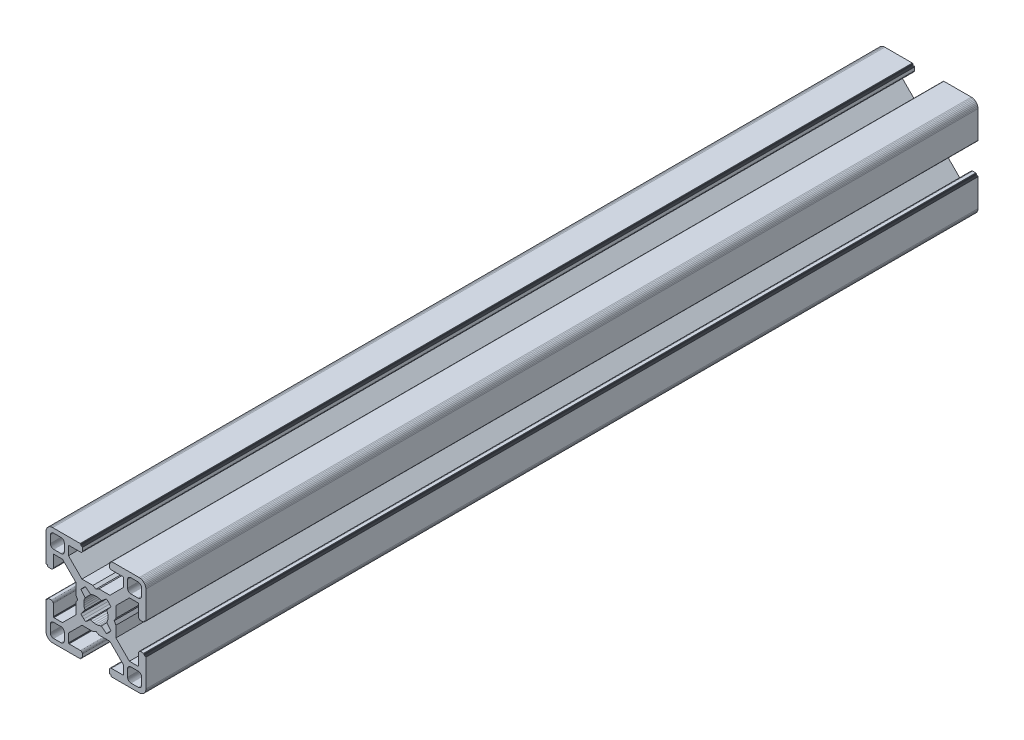
SolidWorks part; units mm, degrees
ref_plane "Front Plane" through (0, 0, 0) normal (0, 0, 1) x (1, 0, 0)
ref_plane "Top Plane" through (0, 0, 0) normal (0, 1, 0) x (1, 0, 0)
ref_plane "Right Plane" through (0, 0, 0) normal (1, 0, 0) x (0, 0, -1)
ref_plane "Plane1" through (0, 0, 0) normal (0, 0, 1) x (1, 0, 0)
sketch "Sketch1" plane through (0, 0, 0) normal (0, 0, 1) x (1, 0, 0)
  line L0 (28.3473, 29.9696) -> (28, 30)
  line L1 (28, 30) -> (19.75, 30)
  line L2 (19.75, 30) -> (19.7153, 29.997)
  line L3 (19.7153, 29.997) -> (19.6816, 29.9879)
  line L4 (19.6816, 29.9879) -> (19.65, 29.9732)
  line L5 (19.65, 29.9732) -> (19.6214, 29.9532)
  line L6 (19.6214, 29.9532) -> (19.5968, 29.9286)
  line L7 (19.5968, 29.9286) -> (19.5768, 29.9)
  line L8 (19.5768, 29.9) -> (19.5621, 29.8684)
  line L9 (19.5621, 29.8684) -> (19.553, 29.8347)
  line L10 (19.553, 29.8347) -> (19.55, 29.8)
  line L11 (19.55, 29.8) -> (19.55, 29.7)
  line L12 (19.55, 29.7) -> (19.547, 29.6653)
  line L13 (19.547, 29.6653) -> (19.5379, 29.6316)
  line L14 (19.5379, 29.6316) -> (19.5232, 29.6)
  line L15 (19.5232, 29.6) -> (19.5032, 29.5714)
  line L16 (19.5032, 29.5714) -> (19.4786, 29.5468)
  line L17 (19.4786, 29.5468) -> (19.45, 29.5268)
  line L18 (19.45, 29.5268) -> (19.4184, 29.5121)
  line L19 (19.4184, 29.5121) -> (19.3847, 29.503)
  line L20 (19.3847, 29.503) -> (19.35, 29.5)
  line L21 (19.35, 29.5) -> (19.25, 29.5)
  line L22 (19.25, 29.5) -> (19.2153, 29.497)
  line L23 (19.2153, 29.497) -> (19.1816, 29.4879)
  line L24 (19.1816, 29.4879) -> (19.15, 29.4732)
  line L25 (19.15, 29.4732) -> (19.1214, 29.4532)
  line L26 (19.1214, 29.4532) -> (19.0968, 29.4286)
  line L27 (19.0968, 29.4286) -> (19.0768, 29.4)
  line L28 (19.0768, 29.4) -> (19.0621, 29.3684)
  line L29 (19.0621, 29.3684) -> (19.053, 29.3347)
  line L30 (19.053, 29.3347) -> (19.05, 29.3)
  line L31 (19.05, 29.3) -> (19.05, 28.4)
  line L32 (19.05, 28.4) -> (19.0591, 28.2958)
  line L33 (19.0591, 28.2958) -> (19.0862, 28.1948)
  line L34 (19.0862, 28.1948) -> (19.1304, 28.1)
  line L35 (19.1304, 28.1) -> (19.1904, 28.0143)
  line L36 (19.1904, 28.0143) -> (19.2643, 27.9404)
  line L37 (19.2643, 27.9404) -> (19.35, 27.8804)
  line L38 (19.35, 27.8804) -> (19.4448, 27.8362)
  line L39 (19.4448, 27.8362) -> (19.5458, 27.8091)
  line L40 (19.5458, 27.8091) -> (19.65, 27.8)
  line L41 (19.65, 27.8) -> (23.05, 27.8)
  line L42 (23.05, 27.8) -> (23.0847, 27.7969)
  line L43 (23.0847, 27.7969) -> (23.1184, 27.7879)
  line L44 (23.1184, 27.7879) -> (23.15, 27.7732)
  line L45 (23.15, 27.7732) -> (23.1786, 27.7532)
  line L46 (23.1786, 27.7532) -> (23.2032, 27.7285)
  line L47 (23.2032, 27.7285) -> (23.2232, 27.7)
  line L48 (23.2232, 27.7) -> (23.2379, 27.6684)
  line L49 (23.2379, 27.6684) -> (23.247, 27.6347)
  line L50 (23.247, 27.6347) -> (23.25, 27.6)
  line L51 (23.25, 27.6) -> (23.25, 25.05)
  line L52 (23.25, 25.05) -> (19.2045, 21)
  line L53 (19.2045, 21) -> (15.9, 21)
  line L54 (15.9, 21) -> (15, 20.4848)
  line L55 (15, 20.4848) -> (14.1, 21)
  line L56 (14.1, 21) -> (10.7955, 21)
  line L57 (10.7955, 21) -> (7.9973, 23.8013)
  line L58 (7.9973, 23.8013) -> (6.75, 25.05)
  line L59 (6.75, 25.05) -> (6.75, 27.6)
  line L60 (6.75, 27.6) -> (6.753, 27.6347)
  line L61 (6.753, 27.6347) -> (6.7621, 27.6684)
  line L62 (6.7621, 27.6684) -> (6.7768, 27.7)
  line L63 (6.7768, 27.7) -> (6.7968, 27.7285)
  line L64 (6.7968, 27.7285) -> (6.8215, 27.7532)
  line L65 (6.8215, 27.7532) -> (6.85, 27.7732)
  line L66 (6.85, 27.7732) -> (6.8816, 27.7879)
  line L67 (6.8816, 27.7879) -> (6.9153, 27.7969)
  line L68 (6.9153, 27.7969) -> (6.95, 27.8)
  line L69 (6.95, 27.8) -> (10.35, 27.8)
  line L70 (10.35, 27.8) -> (10.4542, 27.8091)
  line L71 (10.4542, 27.8091) -> (10.5552, 27.8362)
  line L72 (10.5552, 27.8362) -> (10.65, 27.8804)
  line L73 (10.65, 27.8804) -> (10.7357, 27.9404)
  line L74 (10.7357, 27.9404) -> (10.8096, 28.0143)
  line L75 (10.8096, 28.0143) -> (10.8696, 28.1)
  line L76 (10.8696, 28.1) -> (10.9138, 28.1948)
  line L77 (10.9138, 28.1948) -> (10.9409, 28.2958)
  line L78 (10.9409, 28.2958) -> (10.95, 28.4)
  line L79 (10.95, 28.4) -> (10.95, 29.3)
  line L80 (10.95, 29.3) -> (10.947, 29.3347)
  line L81 (10.947, 29.3347) -> (10.938, 29.3684)
  line L82 (10.938, 29.3684) -> (10.9232, 29.4)
  line L83 (10.9232, 29.4) -> (10.9032, 29.4286)
  line L84 (10.9032, 29.4286) -> (10.8786, 29.4532)
  line L85 (10.8786, 29.4532) -> (10.85, 29.4732)
  line L86 (10.85, 29.4732) -> (10.8184, 29.4879)
  line L87 (10.8184, 29.4879) -> (10.7847, 29.497)
  line L88 (10.7847, 29.497) -> (10.75, 29.5)
  line L89 (10.75, 29.5) -> (10.65, 29.5)
  line L90 (10.65, 29.5) -> (10.6153, 29.503)
  line L91 (10.6153, 29.503) -> (10.5816, 29.5121)
  line L92 (10.5816, 29.5121) -> (10.55, 29.5268)
  line L93 (10.55, 29.5268) -> (10.5214, 29.5468)
  line L94 (10.5214, 29.5468) -> (10.4968, 29.5714)
  line L95 (10.4968, 29.5714) -> (10.4768, 29.6)
  line L96 (10.4768, 29.6) -> (10.4621, 29.6316)
  line L97 (10.4621, 29.6316) -> (10.453, 29.6653)
  line L98 (10.453, 29.6653) -> (10.45, 29.7)
  line L99 (10.45, 29.7) -> (10.45, 29.8)
  line L100 (10.45, 29.8) -> (10.447, 29.8347)
  line L101 (10.447, 29.8347) -> (10.4379, 29.8684)
  line L102 (10.4379, 29.8684) -> (10.4232, 29.9)
  line L103 (10.4232, 29.9) -> (10.4032, 29.9286)
  line L104 (10.4032, 29.9286) -> (10.3786, 29.9532)
  line L105 (10.3786, 29.9532) -> (10.35, 29.9732)
  line L106 (10.35, 29.9732) -> (10.3184, 29.9879)
  line L107 (10.3184, 29.9879) -> (10.2847, 29.997)
  line L108 (10.2847, 29.997) -> (10.25, 30)
  line L109 (10.25, 30) -> (2, 30)
  line L110 (2, 30) -> (1.6527, 29.9696)
  line L111 (1.6527, 29.9696) -> (1.316, 29.8794)
  line L112 (1.316, 29.8794) -> (1, 29.7321)
  line L113 (1, 29.7321) -> (0.7144, 29.5321)
  line L114 (0.7144, 29.5321) -> (0.4679, 29.2856)
  line L115 (0.4679, 29.2856) -> (0.2679, 29)
  line L116 (0.2679, 29) -> (0.1206, 28.684)
  line L117 (0.1206, 28.684) -> (0.0304, 28.3473)
  line L118 (0.0304, 28.3473) -> (0, 28)
  line L119 (0, 28) -> (0, 19.75)
  line L120 (0, 19.75) -> (0.003, 19.7153)
  line L121 (0.003, 19.7153) -> (0.0121, 19.6816)
  line L122 (0.0121, 19.6816) -> (0.0268, 19.65)
  line L123 (0.0268, 19.65) -> (0.0468, 19.6214)
  line L124 (0.0468, 19.6214) -> (0.0714, 19.5968)
  line L125 (0.0714, 19.5968) -> (0.1, 19.5768)
  line L126 (0.1, 19.5768) -> (0.1316, 19.5621)
  line L127 (0.1316, 19.5621) -> (0.1653, 19.553)
  line L128 (0.1653, 19.553) -> (0.2, 19.55)
  line L129 (0.2, 19.55) -> (0.3, 19.55)
  line L130 (0.3, 19.55) -> (0.3347, 19.547)
  line L131 (0.3347, 19.547) -> (0.3684, 19.5379)
  line L132 (0.3684, 19.5379) -> (0.4, 19.5232)
  line L133 (0.4, 19.5232) -> (0.4286, 19.5032)
  line L134 (0.4286, 19.5032) -> (0.4532, 19.4786)
  line L135 (0.4532, 19.4786) -> (0.4732, 19.45)
  line L136 (0.4732, 19.45) -> (0.4879, 19.4184)
  line L137 (0.4879, 19.4184) -> (0.497, 19.3847)
  line L138 (0.497, 19.3847) -> (0.5, 19.35)
  line L139 (0.5, 19.35) -> (0.5, 19.25)
  line L140 (0.5, 19.25) -> (0.503, 19.2153)
  line L141 (0.503, 19.2153) -> (0.5121, 19.1816)
  line L142 (0.5121, 19.1816) -> (0.5268, 19.15)
  line L143 (0.5268, 19.15) -> (0.5468, 19.1214)
  line L144 (0.5468, 19.1214) -> (0.5714, 19.0968)
  line L145 (0.5714, 19.0968) -> (0.6, 19.0768)
  line L146 (0.6, 19.0768) -> (0.6316, 19.0621)
  line L147 (0.6316, 19.0621) -> (0.6653, 19.053)
  line L148 (0.6653, 19.053) -> (0.7, 19.05)
  line L149 (0.7, 19.05) -> (1.6, 19.05)
  line L150 (1.6, 19.05) -> (1.7042, 19.0591)
  line L151 (1.7042, 19.0591) -> (1.8052, 19.0862)
  line L152 (1.8052, 19.0862) -> (1.9, 19.1304)
  line L153 (1.9, 19.1304) -> (1.9857, 19.1904)
  line L154 (1.9857, 19.1904) -> (2.0596, 19.2643)
  line L155 (2.0596, 19.2643) -> (2.1196, 19.35)
  line L156 (2.1196, 19.35) -> (2.1638, 19.4448)
  line L157 (2.1638, 19.4448) -> (2.1909, 19.5458)
  line L158 (2.1909, 19.5458) -> (2.2, 19.65)
  line L159 (2.2, 19.65) -> (2.2, 23.05)
  line L160 (2.2, 23.05) -> (2.203, 23.0847)
  line L161 (2.203, 23.0847) -> (2.2121, 23.1184)
  line L162 (2.2121, 23.1184) -> (2.2268, 23.15)
  line L163 (2.2268, 23.15) -> (2.2468, 23.1786)
  line L164 (2.2468, 23.1786) -> (2.2714, 23.2032)
  line L165 (2.2714, 23.2032) -> (2.3, 23.2232)
  line L166 (2.3, 23.2232) -> (2.3316, 23.2379)
  line L167 (2.3316, 23.2379) -> (2.3653, 23.247)
  line L168 (2.3653, 23.247) -> (2.4, 23.25)
  line L169 (2.4, 23.25) -> (4.95, 23.25)
  line L170 (4.95, 23.25) -> (7.9973, 20.2027)
  line L171 (7.9973, 20.2027) -> (8.9955, 19.2045)
  line L172 (8.9955, 19.2045) -> (8.9955, 15.9)
  line L173 (8.9955, 15.9) -> (9.5151, 15)
  line L174 (9.5151, 15) -> (8.9955, 14.1)
  line L175 (8.9955, 14.1) -> (8.9955, 10.7955)
  line L176 (8.9955, 10.7955) -> (4.95, 6.75)
  line L177 (4.95, 6.75) -> (2.4, 6.75)
  line L178 (2.4, 6.75) -> (2.3653, 6.753)
  line L179 (2.3653, 6.753) -> (2.3316, 6.7621)
  line L180 (2.3316, 6.7621) -> (2.3, 6.7768)
  line L181 (2.3, 6.7768) -> (2.2714, 6.7968)
  line L182 (2.2714, 6.7968) -> (2.2468, 6.8214)
  line L183 (2.2468, 6.8214) -> (2.2268, 6.85)
  line L184 (2.2268, 6.85) -> (2.2121, 6.8816)
  line L185 (2.2121, 6.8816) -> (2.203, 6.9153)
  line L186 (2.203, 6.9153) -> (2.2, 6.95)
  line L187 (2.2, 6.95) -> (2.2, 10.35)
  line L188 (2.2, 10.35) -> (2.1909, 10.4542)
  line L189 (2.1909, 10.4542) -> (2.1638, 10.5552)
  line L190 (2.1638, 10.5552) -> (2.1196, 10.65)
  line L191 (2.1196, 10.65) -> (2.0596, 10.7357)
  line L192 (2.0596, 10.7357) -> (1.9857, 10.8096)
  line L193 (1.9857, 10.8096) -> (1.9, 10.8696)
  line L194 (1.9, 10.8696) -> (1.8052, 10.9138)
  line L195 (1.8052, 10.9138) -> (1.7042, 10.9409)
  line L196 (1.7042, 10.9409) -> (1.6, 10.95)
  line L197 (1.6, 10.95) -> (0.7, 10.95)
  line L198 (0.7, 10.95) -> (0.6653, 10.9469)
  line L199 (0.6653, 10.9469) -> (0.6316, 10.9379)
  line L200 (0.6316, 10.9379) -> (0.6, 10.9232)
  line L201 (0.6, 10.9232) -> (0.5715, 10.9032)
  line L202 (0.5715, 10.9032) -> (0.5468, 10.8785)
  line L203 (0.5468, 10.8785) -> (0.5268, 10.85)
  line L204 (0.5268, 10.85) -> (0.5121, 10.8184)
  line L205 (0.5121, 10.8184) -> (0.503, 10.7847)
  line L206 (0.503, 10.7847) -> (0.5, 10.75)
  line L207 (0.5, 10.75) -> (0.5, 10.65)
  line L208 (0.5, 10.65) -> (0.497, 10.6153)
  line L209 (0.497, 10.6153) -> (0.4879, 10.5816)
  line L210 (0.4879, 10.5816) -> (0.4732, 10.55)
  line L211 (0.4732, 10.55) -> (0.4532, 10.5214)
  line L212 (0.4532, 10.5214) -> (0.4286, 10.4968)
  line L213 (0.4286, 10.4968) -> (0.4, 10.4768)
  line L214 (0.4, 10.4768) -> (0.3684, 10.4621)
  line L215 (0.3684, 10.4621) -> (0.3347, 10.453)
  line L216 (0.3347, 10.453) -> (0.3, 10.45)
  line L217 (0.3, 10.45) -> (0.2, 10.45)
  line L218 (0.2, 10.45) -> (0.1653, 10.447)
  line L219 (0.1653, 10.447) -> (0.1316, 10.4379)
  line L220 (0.1316, 10.4379) -> (0.1, 10.4232)
  line L221 (0.1, 10.4232) -> (0.0714, 10.4032)
  line L222 (0.0714, 10.4032) -> (0.0468, 10.3786)
  line L223 (0.0468, 10.3786) -> (0.0268, 10.35)
  line L224 (0.0268, 10.35) -> (0.0121, 10.3184)
  line L225 (0.0121, 10.3184) -> (0.003, 10.2847)
  line L226 (0.003, 10.2847) -> (0, 10.25)
  line L227 (0, 10.25) -> (0, 2)
  line L228 (0, 2) -> (0.0304, 1.6527)
  line L229 (0.0304, 1.6527) -> (0.1206, 1.316)
  line L230 (0.1206, 1.316) -> (0.2679, 1)
  line L231 (0.2679, 1) -> (0.4679, 0.7144)
  line L232 (0.4679, 0.7144) -> (0.7144, 0.4679)
  line L233 (0.7144, 0.4679) -> (1, 0.2679)
  line L234 (1, 0.2679) -> (1.316, 0.1206)
  line L235 (1.316, 0.1206) -> (1.6527, 0.0304)
  line L236 (1.6527, 0.0304) -> (2, 0)
  line L237 (2, 0) -> (10.25, 0)
  line L238 (10.25, 0) -> (10.2847, 0.003)
  line L239 (10.2847, 0.003) -> (10.3184, 0.0121)
  line L240 (10.3184, 0.0121) -> (10.35, 0.0268)
  line L241 (10.35, 0.0268) -> (10.3786, 0.0468)
  line L242 (10.3786, 0.0468) -> (10.4032, 0.0714)
  line L243 (10.4032, 0.0714) -> (10.4232, 0.1)
  line L244 (10.4232, 0.1) -> (10.4379, 0.1316)
  line L245 (10.4379, 0.1316) -> (10.447, 0.1653)
  line L246 (10.447, 0.1653) -> (10.45, 0.2)
  line L247 (10.45, 0.2) -> (10.45, 0.3)
  line L248 (10.45, 0.3) -> (10.453, 0.3347)
  line L249 (10.453, 0.3347) -> (10.4621, 0.3684)
  line L250 (10.4621, 0.3684) -> (10.4768, 0.4)
  line L251 (10.4768, 0.4) -> (10.4968, 0.4286)
  line L252 (10.4968, 0.4286) -> (10.5214, 0.4532)
  line L253 (10.5214, 0.4532) -> (10.55, 0.4732)
  line L254 (10.55, 0.4732) -> (10.5816, 0.4879)
  line L255 (10.5816, 0.4879) -> (10.6153, 0.497)
  line L256 (10.6153, 0.497) -> (10.65, 0.5)
  line L257 (10.65, 0.5) -> (10.75, 0.5)
  line L258 (10.75, 0.5) -> (10.7847, 0.503)
  line L259 (10.7847, 0.503) -> (10.8184, 0.5121)
  line L260 (10.8184, 0.5121) -> (10.85, 0.5268)
  line L261 (10.85, 0.5268) -> (10.8785, 0.5468)
  line L262 (10.8785, 0.5468) -> (10.9032, 0.5715)
  line L263 (10.9032, 0.5715) -> (10.9232, 0.6)
  line L264 (10.9232, 0.6) -> (10.9379, 0.6316)
  line L265 (10.9379, 0.6316) -> (10.9469, 0.6653)
  line L266 (10.9469, 0.6653) -> (10.95, 0.7)
  line L267 (10.95, 0.7) -> (10.95, 1.6)
  line L268 (10.95, 1.6) -> (10.9409, 1.7042)
  line L269 (10.9409, 1.7042) -> (10.9138, 1.8052)
  line L270 (10.9138, 1.8052) -> (10.8696, 1.9)
  line L271 (10.8696, 1.9) -> (10.8096, 1.9857)
  line L272 (10.8096, 1.9857) -> (10.7357, 2.0596)
  line L273 (10.7357, 2.0596) -> (10.65, 2.1196)
  line L274 (10.65, 2.1196) -> (10.5552, 2.1638)
  line L275 (10.5552, 2.1638) -> (10.4542, 2.1909)
  line L276 (10.4542, 2.1909) -> (10.35, 2.2)
  line L277 (10.35, 2.2) -> (6.95, 2.2)
  line L278 (6.95, 2.2) -> (6.9153, 2.203)
  line L279 (6.9153, 2.203) -> (6.8816, 2.212)
  line L280 (6.8816, 2.212) -> (6.85, 2.2268)
  line L281 (6.85, 2.2268) -> (6.8215, 2.2468)
  line L282 (6.8215, 2.2468) -> (6.7968, 2.2714)
  line L283 (6.7968, 2.2714) -> (6.7768, 2.3)
  line L284 (6.7768, 2.3) -> (6.7621, 2.3316)
  line L285 (6.7621, 2.3316) -> (6.753, 2.3653)
  line L286 (6.753, 2.3653) -> (6.75, 2.4)
  line L287 (6.75, 2.4) -> (6.75, 4.95)
  line L288 (6.75, 4.95) -> (9.7875, 7.9908)
  line L289 (9.7875, 7.9908) -> (10.7955, 9)
  line L290 (10.7955, 9) -> (14.1, 9)
  line L291 (14.1, 9) -> (15, 9.5151)
  line L292 (15, 9.5151) -> (15.9, 9)
  line L293 (15.9, 9) -> (19.2045, 9)
  line L294 (19.2045, 9) -> (20.2126, 7.9908)
  line L295 (20.2126, 7.9908) -> (23.25, 4.95)
  line L296 (23.25, 4.95) -> (23.25, 2.4)
  line L297 (23.25, 2.4) -> (23.247, 2.3653)
  line L298 (23.247, 2.3653) -> (23.2379, 2.3316)
  line L299 (23.2379, 2.3316) -> (23.2232, 2.3)
  line L300 (23.2232, 2.3) -> (23.2032, 2.2714)
  line L301 (23.2032, 2.2714) -> (23.1786, 2.2468)
  line L302 (23.1786, 2.2468) -> (23.15, 2.2268)
  line L303 (23.15, 2.2268) -> (23.1184, 2.212)
  line L304 (23.1184, 2.212) -> (23.0847, 2.203)
  line L305 (23.0847, 2.203) -> (23.05, 2.2)
  line L306 (23.05, 2.2) -> (19.65, 2.2)
  line L307 (19.65, 2.2) -> (19.5458, 2.1909)
  line L308 (19.5458, 2.1909) -> (19.4448, 2.1638)
  line L309 (19.4448, 2.1638) -> (19.35, 2.1196)
  line L310 (19.35, 2.1196) -> (19.2643, 2.0596)
  line L311 (19.2643, 2.0596) -> (19.1904, 1.9857)
  line L312 (19.1904, 1.9857) -> (19.1304, 1.9)
  line L313 (19.1304, 1.9) -> (19.0862, 1.8052)
  line L314 (19.0862, 1.8052) -> (19.0591, 1.7042)
  line L315 (19.0591, 1.7042) -> (19.05, 1.6)
  line L316 (19.05, 1.6) -> (19.05, 0.7)
  line L317 (19.05, 0.7) -> (19.053, 0.6653)
  line L318 (19.053, 0.6653) -> (19.0621, 0.6316)
  line L319 (19.0621, 0.6316) -> (19.0768, 0.6)
  line L320 (19.0768, 0.6) -> (19.0968, 0.5714)
  line L321 (19.0968, 0.5714) -> (19.1214, 0.5468)
  line L322 (19.1214, 0.5468) -> (19.15, 0.5268)
  line L323 (19.15, 0.5268) -> (19.1816, 0.5121)
  line L324 (19.1816, 0.5121) -> (19.2153, 0.503)
  line L325 (19.2153, 0.503) -> (19.25, 0.5)
  line L326 (19.25, 0.5) -> (19.35, 0.5)
  line L327 (19.35, 0.5) -> (19.3847, 0.497)
  line L328 (19.3847, 0.497) -> (19.4184, 0.4879)
  line L329 (19.4184, 0.4879) -> (19.45, 0.4732)
  line L330 (19.45, 0.4732) -> (19.4786, 0.4532)
  line L331 (19.4786, 0.4532) -> (19.5032, 0.4286)
  line L332 (19.5032, 0.4286) -> (19.5232, 0.4)
  line L333 (19.5232, 0.4) -> (19.5379, 0.3684)
  line L334 (19.5379, 0.3684) -> (19.547, 0.3347)
  line L335 (19.547, 0.3347) -> (19.55, 0.3)
  line L336 (19.55, 0.3) -> (19.55, 0.2)
  line L337 (19.55, 0.2) -> (19.553, 0.1653)
  line L338 (19.553, 0.1653) -> (19.5621, 0.1316)
  line L339 (19.5621, 0.1316) -> (19.5768, 0.1)
  line L340 (19.5768, 0.1) -> (19.5968, 0.0714)
  line L341 (19.5968, 0.0714) -> (19.6214, 0.0468)
  line L342 (19.6214, 0.0468) -> (19.65, 0.0268)
  line L343 (19.65, 0.0268) -> (19.6816, 0.0121)
  line L344 (19.6816, 0.0121) -> (19.7153, 0.003)
  line L345 (19.7153, 0.003) -> (19.75, 0)
  line L346 (19.75, 0) -> (28, 0)
  line L347 (28, 0) -> (28.3473, 0.0304)
  line L348 (28.3473, 0.0304) -> (28.684, 0.1206)
  line L349 (28.684, 0.1206) -> (29, 0.2679)
  line L350 (29, 0.2679) -> (29.2856, 0.4679)
  line L351 (29.2856, 0.4679) -> (29.5321, 0.7144)
  line L352 (29.5321, 0.7144) -> (29.7321, 1)
  line L353 (29.7321, 1) -> (29.8794, 1.316)
  line L354 (29.8794, 1.316) -> (29.9696, 1.6527)
  line L355 (29.9696, 1.6527) -> (30, 2)
  line L356 (30, 2) -> (30, 10.25)
  line L357 (30, 10.25) -> (29.997, 10.2847)
  line L358 (29.997, 10.2847) -> (29.988, 10.3184)
  line L359 (29.988, 10.3184) -> (29.9732, 10.35)
  line L360 (29.9732, 10.35) -> (29.9532, 10.3785)
  line L361 (29.9532, 10.3785) -> (29.9286, 10.4032)
  line L362 (29.9286, 10.4032) -> (29.9, 10.4232)
  line L363 (29.9, 10.4232) -> (29.8684, 10.4379)
  line L364 (29.8684, 10.4379) -> (29.8347, 10.447)
  line L365 (29.8347, 10.447) -> (29.8, 10.45)
  line L366 (29.8, 10.45) -> (29.7, 10.45)
  line L367 (29.7, 10.45) -> (29.6649, 10.4534)
  line L368 (29.6649, 10.4534) -> (29.6312, 10.4624)
  line L369 (29.6312, 10.4624) -> (29.5996, 10.4772)
  line L370 (29.5996, 10.4772) -> (29.5711, 10.4972)
  line L371 (29.5711, 10.4972) -> (29.5464, 10.5218)
  line L372 (29.5464, 10.5218) -> (29.5264, 10.5504)
  line L373 (29.5264, 10.5504) -> (29.5117, 10.582)
  line L374 (29.5117, 10.582) -> (29.5027, 10.6156)
  line L375 (29.5027, 10.6156) -> (29.4996, 10.6504)
  line L376 (29.4996, 10.6504) -> (29.4996, 10.7504)
  line L377 (29.4996, 10.7504) -> (29.497, 10.7847)
  line L378 (29.497, 10.7847) -> (29.4879, 10.8184)
  line L379 (29.4879, 10.8184) -> (29.4732, 10.85)
  line L380 (29.4732, 10.85) -> (29.4532, 10.8785)
  line L381 (29.4532, 10.8785) -> (29.4286, 10.9032)
  line L382 (29.4286, 10.9032) -> (29.4, 10.9232)
  line L383 (29.4, 10.9232) -> (29.3684, 10.9379)
  line L384 (29.3684, 10.9379) -> (29.3347, 10.9469)
  line L385 (29.3347, 10.9469) -> (29.3, 10.95)
  line L386 (29.3, 10.95) -> (28.4, 10.95)
  line L387 (28.4, 10.95) -> (28.2958, 10.9409)
  line L388 (28.2958, 10.9409) -> (28.1948, 10.9138)
  line L389 (28.1948, 10.9138) -> (28.1, 10.8696)
  line L390 (28.1, 10.8696) -> (28.0143, 10.8096)
  line L391 (28.0143, 10.8096) -> (27.9404, 10.7357)
  line L392 (27.9404, 10.7357) -> (27.8804, 10.65)
  line L393 (27.8804, 10.65) -> (27.8362, 10.5552)
  line L394 (27.8362, 10.5552) -> (27.8091, 10.4542)
  line L395 (27.8091, 10.4542) -> (27.8, 10.35)
  line L396 (27.8, 10.35) -> (27.8, 6.95)
  line L397 (27.8, 6.95) -> (27.797, 6.9153)
  line L398 (27.797, 6.9153) -> (27.7879, 6.8816)
  line L399 (27.7879, 6.8816) -> (27.7732, 6.85)
  line L400 (27.7732, 6.85) -> (27.7532, 6.8214)
  line L401 (27.7532, 6.8214) -> (27.7286, 6.7968)
  line L402 (27.7286, 6.7968) -> (27.7, 6.7768)
  line L403 (27.7, 6.7768) -> (27.6684, 6.7621)
  line L404 (27.6684, 6.7621) -> (27.6347, 6.753)
  line L405 (27.6347, 6.753) -> (27.6, 6.75)
  line L406 (27.6, 6.75) -> (25.05, 6.75)
  line L407 (25.05, 6.75) -> (23.8092, 7.9908)
  line L408 (23.8092, 7.9908) -> (21.0045, 10.7955)
  line L409 (21.0045, 10.7955) -> (21.0045, 14.1)
  line L410 (21.0045, 14.1) -> (20.4849, 15)
  line L411 (20.4849, 15) -> (21.0045, 15.9)
  line L412 (21.0045, 15.9) -> (21.0045, 19.2045)
  line L413 (21.0045, 19.2045) -> (25.05, 23.25)
  line L414 (25.05, 23.25) -> (27.6, 23.25)
  line L415 (27.6, 23.25) -> (27.6347, 23.247)
  line L416 (27.6347, 23.247) -> (27.6684, 23.2379)
  line L417 (27.6684, 23.2379) -> (27.7, 23.2232)
  line L418 (27.7, 23.2232) -> (27.7286, 23.2032)
  line L419 (27.7286, 23.2032) -> (27.7532, 23.1786)
  line L420 (27.7532, 23.1786) -> (27.7732, 23.15)
  line L421 (27.7732, 23.15) -> (27.7879, 23.1184)
  line L422 (27.7879, 23.1184) -> (27.797, 23.0847)
  line L423 (27.797, 23.0847) -> (27.8, 23.05)
  line L424 (27.8, 23.05) -> (27.8, 19.65)
  line L425 (27.8, 19.65) -> (27.8091, 19.5458)
  line L426 (27.8091, 19.5458) -> (27.8362, 19.4448)
  line L427 (27.8362, 19.4448) -> (27.8804, 19.35)
  line L428 (27.8804, 19.35) -> (27.9404, 19.2643)
  line L429 (27.9404, 19.2643) -> (28.0143, 19.1904)
  line L430 (28.0143, 19.1904) -> (28.1, 19.1304)
  line L431 (28.1, 19.1304) -> (28.1948, 19.0862)
  line L432 (28.1948, 19.0862) -> (28.2958, 19.0591)
  line L433 (28.2958, 19.0591) -> (28.4, 19.05)
  line L434 (28.4, 19.05) -> (29.3, 19.05)
  line L435 (29.3, 19.05) -> (29.3347, 19.053)
  line L436 (29.3347, 19.053) -> (29.3684, 19.0621)
  line L437 (29.3684, 19.0621) -> (29.4, 19.0768)
  line L438 (29.4, 19.0768) -> (29.4282, 19.0971)
  line L439 (29.4282, 19.0971) -> (29.4528, 19.1218)
  line L440 (29.4528, 19.1218) -> (29.4728, 19.1504)
  line L441 (29.4728, 19.1504) -> (29.4876, 19.182)
  line L442 (29.4876, 19.182) -> (29.4966, 19.2156)
  line L443 (29.4966, 19.2156) -> (29.4996, 19.2504)
  line L444 (29.4996, 19.2504) -> (29.4996, 19.3504)
  line L445 (29.4996, 19.3504) -> (29.5027, 19.3851)
  line L446 (29.5027, 19.3851) -> (29.5117, 19.4188)
  line L447 (29.5117, 19.4188) -> (29.5264, 19.4504)
  line L448 (29.5264, 19.4504) -> (29.5464, 19.4789)
  line L449 (29.5464, 19.4789) -> (29.5711, 19.5036)
  line L450 (29.5711, 19.5036) -> (29.5996, 19.5236)
  line L451 (29.5996, 19.5236) -> (29.6312, 19.5383)
  line L452 (29.6312, 19.5383) -> (29.6649, 19.5473)
  line L453 (29.6649, 19.5473) -> (29.7, 19.55)
  line L454 (29.7, 19.55) -> (29.8, 19.55)
  line L455 (29.8, 19.55) -> (29.8347, 19.553)
  line L456 (29.8347, 19.553) -> (29.8684, 19.5621)
  line L457 (29.8684, 19.5621) -> (29.9, 19.5768)
  line L458 (29.9, 19.5768) -> (29.9286, 19.5968)
  line L459 (29.9286, 19.5968) -> (29.9532, 19.6214)
  line L460 (29.9532, 19.6214) -> (29.9732, 19.65)
  line L461 (29.9732, 19.65) -> (29.9879, 19.6816)
  line L462 (29.9879, 19.6816) -> (29.997, 19.7153)
  line L463 (29.997, 19.7153) -> (30, 19.75)
  line L464 (30, 19.75) -> (30, 28)
  line L465 (30, 28) -> (29.9696, 28.3473)
  line L466 (29.9696, 28.3473) -> (29.8794, 28.684)
  line L467 (29.8794, 28.684) -> (29.7321, 29)
  line L468 (29.7321, 29) -> (29.5321, 29.2856)
  line L469 (29.5321, 29.2856) -> (29.2856, 29.5321)
  line L470 (29.2856, 29.5321) -> (29, 29.7321)
  line L471 (29, 29.7321) -> (28.684, 29.8794)
  line L472 (28.684, 29.8794) -> (28.3473, 29.9696)
  line L473 (1.3, 25.5) -> (1.3, 27.7)
  line L474 (1.3, 27.7) -> (1.3123, 27.8564)
  line L475 (1.3123, 27.8564) -> (1.3489, 28.009)
  line L476 (1.3489, 28.009) -> (1.409, 28.154)
  line L477 (1.409, 28.154) -> (1.491, 28.2878)
  line L478 (1.491, 28.2878) -> (1.5929, 28.4071)
  line L479 (1.5929, 28.4071) -> (1.7122, 28.509)
  line L480 (1.7122, 28.509) -> (1.846, 28.591)
  line L481 (1.846, 28.591) -> (1.991, 28.6511)
  line L482 (1.991, 28.6511) -> (2.1436, 28.6877)
  line L483 (2.1436, 28.6877) -> (2.3, 28.7)
  line L484 (2.3, 28.7) -> (4.5, 28.7)
  line L485 (4.5, 28.7) -> (4.6564, 28.6877)
  line L486 (4.6564, 28.6877) -> (4.809, 28.6511)
  line L487 (4.809, 28.6511) -> (4.954, 28.591)
  line L488 (4.954, 28.591) -> (5.0878, 28.509)
  line L489 (5.0878, 28.509) -> (5.2071, 28.4071)
  line L490 (5.2071, 28.4071) -> (5.309, 28.2878)
  line L491 (5.309, 28.2878) -> (5.391, 28.154)
  line L492 (5.391, 28.154) -> (5.4511, 28.009)
  line L493 (5.4511, 28.009) -> (5.4877, 27.8564)
  line L494 (5.4877, 27.8564) -> (5.5, 27.7)
  line L495 (5.5, 27.7) -> (5.5, 25.5)
  line L496 (5.5, 25.5) -> (5.4877, 25.3436)
  line L497 (5.4877, 25.3436) -> (5.4511, 25.191)
  line L498 (5.4511, 25.191) -> (5.391, 25.046)
  line L499 (5.391, 25.046) -> (5.309, 24.9122)
  line L500 (5.309, 24.9122) -> (5.2071, 24.7929)
  line L501 (5.2071, 24.7929) -> (5.0878, 24.691)
  line L502 (5.0878, 24.691) -> (4.954, 24.609)
  line L503 (4.954, 24.609) -> (4.809, 24.5489)
  line L504 (4.809, 24.5489) -> (4.6564, 24.5123)
  line L505 (4.6564, 24.5123) -> (4.5, 24.5)
  line L506 (4.5, 24.5) -> (2.3, 24.5)
  line L507 (2.3, 24.5) -> (2.1436, 24.5123)
  line L508 (2.1436, 24.5123) -> (1.991, 24.5489)
  line L509 (1.991, 24.5489) -> (1.846, 24.609)
  line L510 (1.846, 24.609) -> (1.7122, 24.691)
  line L511 (1.7122, 24.691) -> (1.5929, 24.7929)
  line L512 (1.5929, 24.7929) -> (1.491, 24.9122)
  line L513 (1.491, 24.9122) -> (1.409, 25.046)
  line L514 (1.409, 25.046) -> (1.3489, 25.191)
  line L515 (1.3489, 25.191) -> (1.3123, 25.3436)
  line L516 (1.3123, 25.3436) -> (1.3, 25.5)
  line L517 (25.3436, 28.6877) -> (25.5, 28.7)
  line L518 (25.5, 28.7) -> (27.7, 28.7)
  line L519 (27.7, 28.7) -> (27.8564, 28.6877)
  line L520 (27.8564, 28.6877) -> (28.009, 28.6511)
  line L521 (28.009, 28.6511) -> (28.154, 28.591)
  line L522 (28.154, 28.591) -> (28.2878, 28.509)
  line L523 (28.2878, 28.509) -> (28.4071, 28.4071)
  line L524 (28.4071, 28.4071) -> (28.509, 28.2878)
  line L525 (28.509, 28.2878) -> (28.591, 28.154)
  line L526 (28.591, 28.154) -> (28.6511, 28.009)
  line L527 (28.6511, 28.009) -> (28.6877, 27.8564)
  line L528 (28.6877, 27.8564) -> (28.7, 27.7)
  line L529 (28.7, 27.7) -> (28.7, 25.5)
  line L530 (28.7, 25.5) -> (28.6877, 25.3436)
  line L531 (28.6877, 25.3436) -> (28.6511, 25.191)
  line L532 (28.6511, 25.191) -> (28.591, 25.046)
  line L533 (28.591, 25.046) -> (28.509, 24.9122)
  line L534 (28.509, 24.9122) -> (28.4071, 24.7929)
  line L535 (28.4071, 24.7929) -> (28.2878, 24.691)
  line L536 (28.2878, 24.691) -> (28.154, 24.609)
  line L537 (28.154, 24.609) -> (28.009, 24.5489)
  line L538 (28.009, 24.5489) -> (27.8564, 24.5123)
  line L539 (27.8564, 24.5123) -> (27.7, 24.5)
  line L540 (27.7, 24.5) -> (25.5, 24.5)
  line L541 (25.5, 24.5) -> (25.3436, 24.5123)
  line L542 (25.3436, 24.5123) -> (25.191, 24.5489)
  line L543 (25.191, 24.5489) -> (25.046, 24.609)
  line L544 (25.046, 24.609) -> (24.9122, 24.691)
  line L545 (24.9122, 24.691) -> (24.7929, 24.7929)
  line L546 (24.7929, 24.7929) -> (24.691, 24.9122)
  line L547 (24.691, 24.9122) -> (24.609, 25.046)
  line L548 (24.609, 25.046) -> (24.5489, 25.191)
  line L549 (24.5489, 25.191) -> (24.5123, 25.3436)
  line L550 (24.5123, 25.3436) -> (24.5, 25.5)
  line L551 (24.5, 25.5) -> (24.5, 27.7)
  line L552 (24.5, 27.7) -> (24.5123, 27.8564)
  line L553 (24.5123, 27.8564) -> (24.5489, 28.009)
  line L554 (24.5489, 28.009) -> (24.609, 28.154)
  line L555 (24.609, 28.154) -> (24.691, 28.2878)
  line L556 (24.691, 28.2878) -> (24.7929, 28.4071)
  line L557 (24.7929, 28.4071) -> (24.9122, 28.509)
  line L558 (24.9122, 28.509) -> (25.046, 28.591)
  line L559 (25.046, 28.591) -> (25.191, 28.6511)
  line L560 (25.191, 28.6511) -> (25.3436, 28.6877)
  line L561 (15, 18.65) -> (15.55, 18.6083)
  line L562 (15.55, 18.6083) -> (16.0875, 18.4842)
  line L563 (16.0875, 18.4842) -> (16.6001, 18.2806)
  line L564 (16.6001, 18.2806) -> (18.1359, 19.5184)
  line L565 (18.1359, 19.5184) -> (18.645, 19.1187)
  line L566 (18.645, 19.1187) -> (19.1036, 18.6621)
  line L567 (19.1036, 18.6621) -> (19.5053, 18.1547)
  line L568 (19.5053, 18.1547) -> (18.2806, 16.6001)
  line L569 (18.2806, 16.6001) -> (18.4842, 16.0875)
  line L570 (18.4842, 16.0875) -> (18.6083, 15.55)
  line L571 (18.6083, 15.55) -> (18.65, 15)
  line L572 (18.65, 15) -> (18.6083, 14.45)
  line L573 (18.6083, 14.45) -> (18.4842, 13.9125)
  line L574 (18.4842, 13.9125) -> (18.2806, 13.3999)
  line L575 (18.2806, 13.3999) -> (19.5053, 11.8453)
  line L576 (19.5053, 11.8453) -> (19.1036, 11.3379)
  line L577 (19.1036, 11.3379) -> (18.645, 10.8813)
  line L578 (18.645, 10.8813) -> (18.1359, 10.4816)
  line L579 (18.1359, 10.4816) -> (16.6001, 11.7194)
  line L580 (16.6001, 11.7194) -> (16.0875, 11.5158)
  line L581 (16.0875, 11.5158) -> (15.55, 11.3917)
  line L582 (15.55, 11.3917) -> (15, 11.35)
  line L583 (15, 11.35) -> (14.45, 11.3917)
  line L584 (14.45, 11.3917) -> (13.9125, 11.5158)
  line L585 (13.9125, 11.5158) -> (13.3999, 11.7194)
  line L586 (13.3999, 11.7194) -> (11.8641, 10.4816)
  line L587 (11.8641, 10.4816) -> (11.355, 10.8813)
  line L588 (11.355, 10.8813) -> (10.8964, 11.3379)
  line L589 (10.8964, 11.3379) -> (10.4947, 11.8453)
  line L590 (10.4947, 11.8453) -> (11.7194, 13.3999)
  line L591 (11.7194, 13.3999) -> (11.5158, 13.9125)
  line L592 (11.5158, 13.9125) -> (11.3917, 14.45)
  line L593 (11.3917, 14.45) -> (11.35, 15)
  line L594 (11.35, 15) -> (11.3917, 15.55)
  line L595 (11.3917, 15.55) -> (11.5158, 16.0875)
  line L596 (11.5158, 16.0875) -> (11.7194, 16.6001)
  line L597 (11.7194, 16.6001) -> (10.4947, 18.1547)
  line L598 (10.4947, 18.1547) -> (10.8964, 18.6621)
  line L599 (10.8964, 18.6621) -> (11.355, 19.1187)
  line L600 (11.355, 19.1187) -> (11.8641, 19.5184)
  line L601 (11.8641, 19.5184) -> (13.3999, 18.2806)
  line L602 (13.3999, 18.2806) -> (13.9125, 18.4842)
  line L603 (13.9125, 18.4842) -> (14.45, 18.6083)
  line L604 (14.45, 18.6083) -> (15, 18.65)
  line L605 (4.5, 1.3) -> (2.3, 1.3)
  line L606 (2.3, 1.3) -> (2.1436, 1.3123)
  line L607 (2.1436, 1.3123) -> (1.991, 1.3489)
  line L608 (1.991, 1.3489) -> (1.846, 1.409)
  line L609 (1.846, 1.409) -> (1.7122, 1.491)
  line L610 (1.7122, 1.491) -> (1.5929, 1.5929)
  line L611 (1.5929, 1.5929) -> (1.491, 1.7122)
  line L612 (1.491, 1.7122) -> (1.409, 1.846)
  line L613 (1.409, 1.846) -> (1.3489, 1.991)
  line L614 (1.3489, 1.991) -> (1.3123, 2.1436)
  line L615 (1.3123, 2.1436) -> (1.3, 2.3)
  line L616 (1.3, 2.3) -> (1.3, 4.5)
  line L617 (1.3, 4.5) -> (1.3123, 4.6564)
  line L618 (1.3123, 4.6564) -> (1.3489, 4.809)
  line L619 (1.3489, 4.809) -> (1.409, 4.954)
  line L620 (1.409, 4.954) -> (1.491, 5.0878)
  line L621 (1.491, 5.0878) -> (1.5929, 5.2071)
  line L622 (1.5929, 5.2071) -> (1.7122, 5.309)
  line L623 (1.7122, 5.309) -> (1.846, 5.391)
  line L624 (1.846, 5.391) -> (1.991, 5.4511)
  line L625 (1.991, 5.4511) -> (2.1436, 5.4877)
  line L626 (2.1436, 5.4877) -> (2.3, 5.5)
  line L627 (2.3, 5.5) -> (4.5, 5.5)
  line L628 (4.5, 5.5) -> (4.6564, 5.4877)
  line L629 (4.6564, 5.4877) -> (4.809, 5.4511)
  line L630 (4.809, 5.4511) -> (4.954, 5.391)
  line L631 (4.954, 5.391) -> (5.0878, 5.309)
  line L632 (5.0878, 5.309) -> (5.2071, 5.2071)
  line L633 (5.2071, 5.2071) -> (5.309, 5.0878)
  line L634 (5.309, 5.0878) -> (5.391, 4.954)
  line L635 (5.391, 4.954) -> (5.4511, 4.809)
  line L636 (5.4511, 4.809) -> (5.4877, 4.6564)
  line L637 (5.4877, 4.6564) -> (5.5, 4.5)
  line L638 (5.5, 4.5) -> (5.5, 2.3)
  line L639 (5.5, 2.3) -> (5.4877, 2.1436)
  line L640 (5.4877, 2.1436) -> (5.4511, 1.991)
  line L641 (5.4511, 1.991) -> (5.391, 1.846)
  line L642 (5.391, 1.846) -> (5.309, 1.7122)
  line L643 (5.309, 1.7122) -> (5.2071, 1.5929)
  line L644 (5.2071, 1.5929) -> (5.0878, 1.491)
  line L645 (5.0878, 1.491) -> (4.954, 1.409)
  line L646 (4.954, 1.409) -> (4.809, 1.3489)
  line L647 (4.809, 1.3489) -> (4.6564, 1.3123)
  line L648 (4.6564, 1.3123) -> (4.5, 1.3)
  line L649 (27.7, 1.3) -> (25.5, 1.3)
  line L650 (25.5, 1.3) -> (25.3436, 1.3123)
  line L651 (25.3436, 1.3123) -> (25.191, 1.3489)
  line L652 (25.191, 1.3489) -> (25.046, 1.409)
  line L653 (25.046, 1.409) -> (24.9122, 1.491)
  line L654 (24.9122, 1.491) -> (24.7929, 1.5929)
  line L655 (24.7929, 1.5929) -> (24.691, 1.7122)
  line L656 (24.691, 1.7122) -> (24.609, 1.846)
  line L657 (24.609, 1.846) -> (24.5489, 1.991)
  line L658 (24.5489, 1.991) -> (24.5123, 2.1436)
  line L659 (24.5123, 2.1436) -> (24.5, 2.3)
  line L660 (24.5, 2.3) -> (24.5, 4.5)
  line L661 (24.5, 4.5) -> (24.5123, 4.6564)
  line L662 (24.5123, 4.6564) -> (24.5489, 4.809)
  line L663 (24.5489, 4.809) -> (24.609, 4.954)
  line L664 (24.609, 4.954) -> (24.691, 5.0878)
  line L665 (24.691, 5.0878) -> (24.7929, 5.2071)
  line L666 (24.7929, 5.2071) -> (24.9122, 5.309)
  line L667 (24.9122, 5.309) -> (25.046, 5.391)
  line L668 (25.046, 5.391) -> (25.191, 5.4511)
  line L669 (25.191, 5.4511) -> (25.3436, 5.4877)
  line L670 (25.3436, 5.4877) -> (25.5, 5.5)
  line L671 (25.5, 5.5) -> (27.7, 5.5)
  line L672 (27.7, 5.5) -> (27.8564, 5.4877)
  line L673 (27.8564, 5.4877) -> (28.009, 5.4511)
  line L674 (28.009, 5.4511) -> (28.154, 5.391)
  line L675 (28.154, 5.391) -> (28.2878, 5.309)
  line L676 (28.2878, 5.309) -> (28.4071, 5.2071)
  line L677 (28.4071, 5.2071) -> (28.509, 5.0878)
  line L678 (28.509, 5.0878) -> (28.591, 4.954)
  line L679 (28.591, 4.954) -> (28.6511, 4.809)
  line L680 (28.6511, 4.809) -> (28.6877, 4.6564)
  line L681 (28.6877, 4.6564) -> (28.7, 4.5)
  line L682 (28.7, 4.5) -> (28.7, 2.3)
  line L683 (28.7, 2.3) -> (28.6877, 2.1436)
  line L684 (28.6877, 2.1436) -> (28.6511, 1.991)
  line L685 (28.6511, 1.991) -> (28.591, 1.846)
  line L686 (28.591, 1.846) -> (28.509, 1.7122)
  line L687 (28.509, 1.7122) -> (28.4071, 1.5929)
  line L688 (28.4071, 1.5929) -> (28.2878, 1.491)
  line L689 (28.2878, 1.491) -> (28.154, 1.409)
  line L690 (28.154, 1.409) -> (28.009, 1.3489)
  line L691 (28.009, 1.3489) -> (27.8564, 1.3123)
  line L692 (27.8564, 1.3123) -> (27.7, 1.3)
extrude "Boss-Extrude1" add sketch "Sketch1" against normal blind 250
